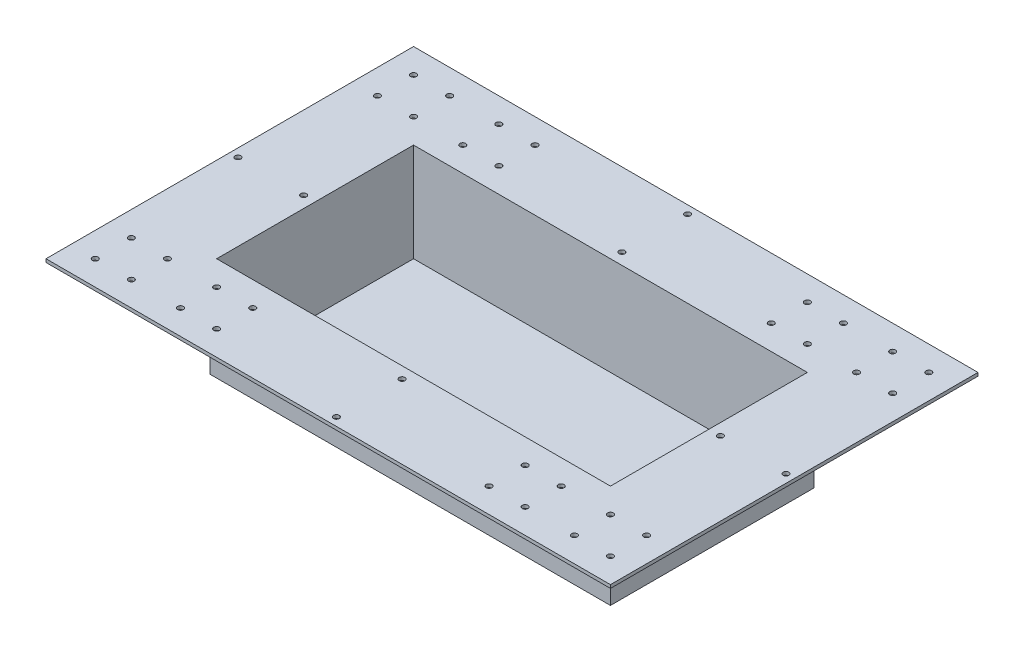
SolidWorks part; units mm, degrees
ref_plane "Front Plane" through (0, 0, 0) normal (0, 0, 1) x (1, 0, 0)
ref_plane "Top Plane" through (0, 0, 0) normal (0, 1, 0) x (1, 0, 0)
ref_plane "Right Plane" through (0, 0, 0) normal (1, 0, 0) x (0, 0, -1)
sketch "Sketch1" plane through (0, 0, 0) normal (0, 1, 0) x (1, 0, 0)
  line L0 (-304.8, 0) -> (304.8, 0) construction
  line L1 (-304.8, 152.4) -> (304.8, 152.4)
  line L2 (-304.8, 152.4) -> (-304.8, -152.4)
  line L3 (-304.8, -152.4) -> (304.8, -152.4)
  line L4 (304.8, 152.4) -> (304.8, -152.4)
  dimension "D1" = 609.6
  dimension "D2" = 304.8
extrude "Extrude-Thin1" add sketch "Sketch1" against normal blind 152.4 thin thin type one direction wall 5.08
sketch "Sketch2" plane through (0, 0, 0) normal (0, 1, 0) x (1, 0, 0)
  line L0 (309.88, -157.48) -> (309.88, 157.48) construction
  line L1 (-436.88, 284.48) -> (436.88, 284.48)
  line L2 (-436.88, 284.48) -> (-436.88, -284.48)
  line L3 (-436.88, -284.48) -> (436.88, -284.48)
  line L4 (436.88, 284.48) -> (436.88, -284.48)
  line L5 (-309.88, -157.48) -> (309.88, -157.48) construction
  line L6 (-309.88, 157.48) -> (-309.88, -157.48) construction
  line L7 (309.88, 157.48) -> (-309.88, 157.48) construction
  line L8 (309.88, -157.48) -> (309.88, 157.48)
  line L9 (-309.88, -157.48) -> (309.88, -157.48)
  line L10 (-309.88, 157.48) -> (-309.88, -157.48)
  line L11 (309.88, 157.48) -> (-309.88, 157.48)
  dimension "D1" = 127
  dimension "D2" = 127
  dimension "D3" = 127
  dimension "D4" = 127
extrude "Boss-Extrude1" add sketch "Sketch2" against normal blind 5.08
sketch "Sketch3" plane through (0, -152.4, 0) normal (0, -1, 0) x (1, 0, 0)
  line L1 (-309.88, 157.48) -> (309.88, 157.48)
  line L2 (-309.88, 157.48) -> (-309.88, -157.48)
  line L3 (-309.88, -157.48) -> (309.88, -157.48)
  line L4 (309.88, 157.48) -> (309.88, -157.48)
extrude "Boss-Extrude2" add sketch "Sketch3" along normal blind 2.54
sketch "Sketch4" plane through (0, 0, 0) normal (0, 1, 0) x (1, 0, 0)
  line L0 (-304.8, 284.48) -> (-304.8, -284.48) construction
  line L1 (436.88, 284.48) -> (-436.88, 284.48) construction
  line L2 (-436.88, -284.48) -> (436.88, -284.48) construction
  line L3 (-304.8, 152.4) -> (-304.8, -152.4) construction
  line L4 (304.8, 284.48) -> (304.8, -284.48) construction
  line L5 (304.8, -152.4) -> (304.8, 152.4) construction
  line L6 (-436.88, -152.4) -> (436.88, -152.4) construction
  line L7 (-436.88, 284.48) -> (-436.88, -284.48) construction
  line L8 (436.88, -284.48) -> (436.88, 284.48) construction
  line L9 (-304.8, -152.4) -> (304.8, -152.4) construction
  line L10 (-436.88, 152.4) -> (436.88, 152.4) construction
  line L11 (304.8, 152.4) -> (-304.8, 152.4) construction
  line L12 (-436.88, 284.48) -> (-304.8, 152.4) construction
  line L13 (-304.8, 284.48) -> (-436.88, 152.4) construction
  line L14 (-398.78, 246.38) -> (-342.9, 246.38) construction
  line L15 (-398.78, 246.38) -> (-398.78, 190.5) construction
  line L16 (-398.78, 190.5) -> (-342.9, 190.5) construction
  line L17 (-342.9, 246.38) -> (-342.9, 190.5) construction
  line L18 (-436.88, 0) -> (436.88, 0) construction
  line L19 (0, 284.48) -> (0, -284.48) construction
  circle A0 centre (-398.78, 246.38) radius 4.445
  circle A1 centre (-342.9, 246.38) radius 4.445
  circle A2 centre (-342.9, 190.5) radius 4.445
  circle A3 centre (-398.78, 190.5) radius 4.445
  circle A4 centre (-266.7, 246.38) radius 4.445
  circle A5 centre (-266.7, 190.5) radius 4.445
  circle A6 centre (-210.82, 190.5) radius 4.445
  circle A7 centre (-210.82, 246.38) radius 4.445
  circle A8 centre (-210.82, -190.5) radius 4.445
  circle A9 centre (-210.82, -246.38) radius 4.445
  circle A10 centre (-266.7, -246.38) radius 4.445
  circle A11 centre (-266.7, -190.5) radius 4.445
  circle A12 centre (-398.78, -190.5) radius 4.445
  circle A13 centre (-342.9, -190.5) radius 4.445
  circle A14 centre (-342.9, -246.38) radius 4.445
  circle A15 centre (-398.78, -246.38) radius 4.445
  circle A16 centre (210.82, -246.38) radius 4.445
  circle A17 centre (210.82, -190.5) radius 4.445
  circle A18 centre (266.7, -190.5) radius 4.445
  circle A19 centre (266.7, -246.38) radius 4.445
  circle A20 centre (398.78, -246.38) radius 4.445
  circle A21 centre (342.9, -246.38) radius 4.445
  circle A22 centre (342.9, -190.5) radius 4.445
  circle A23 centre (398.78, -190.5) radius 4.445
  circle A24 centre (398.78, 190.5) radius 4.445
  circle A25 centre (342.9, 190.5) radius 4.445
  circle A26 centre (266.7, 190.5) radius 4.445
  circle A27 centre (210.82, 190.5) radius 4.445
  circle A28 centre (210.82, 246.38) radius 4.445
  circle A29 centre (266.7, 246.38) radius 4.445
  circle A30 centre (342.9, 246.38) radius 4.445
  circle A31 centre (398.78, 246.38) radius 4.445
  circle A32 centre (0, 271.78) radius 4.445
  circle A33 centre (0, 170.18) radius 4.445
  circle A34 centre (-424.18, 0) radius 4.445
  circle A35 centre (-322.58, 0) radius 4.445
  circle A36 centre (0, -271.78) radius 4.445
  circle A37 centre (0, -170.18) radius 4.445
  circle A38 centre (424.18, 0) radius 4.445
  circle A39 centre (322.58, 0) radius 4.445
  point P112 (0, 0)
  dimension "D2" = 8.89
  dimension "D4" = 101.6
  dimension "D5" = 12.7
  dimension "D6" = 101.6
  dimension "D7" = 12.7
  dimension "D8" = 101.6
  dimension "D9" = 101.6
  dimension "D10" = 12.7
  dimension "D1" = 38.1
  dimension "D3" = 12.7
extrude "Cut-Extrude1" cut sketch "Sketch4" against normal through all
sketch "Sketch5" plane through (0, 0, 0) normal (0, 1, 0) x (1, 0, 0)
  line L0 (304.8, 284.48) -> (304.8, -284.48)
  line L1 (436.88, 284.48) -> (-436.88, 284.48) construction
  line L2 (-436.88, -284.48) -> (436.88, -284.48) construction
  line L3 (-304.8, 284.48) -> (-304.8, -284.48)
  line L4 (-304.8, 152.4) -> (-304.8, -152.4) construction
